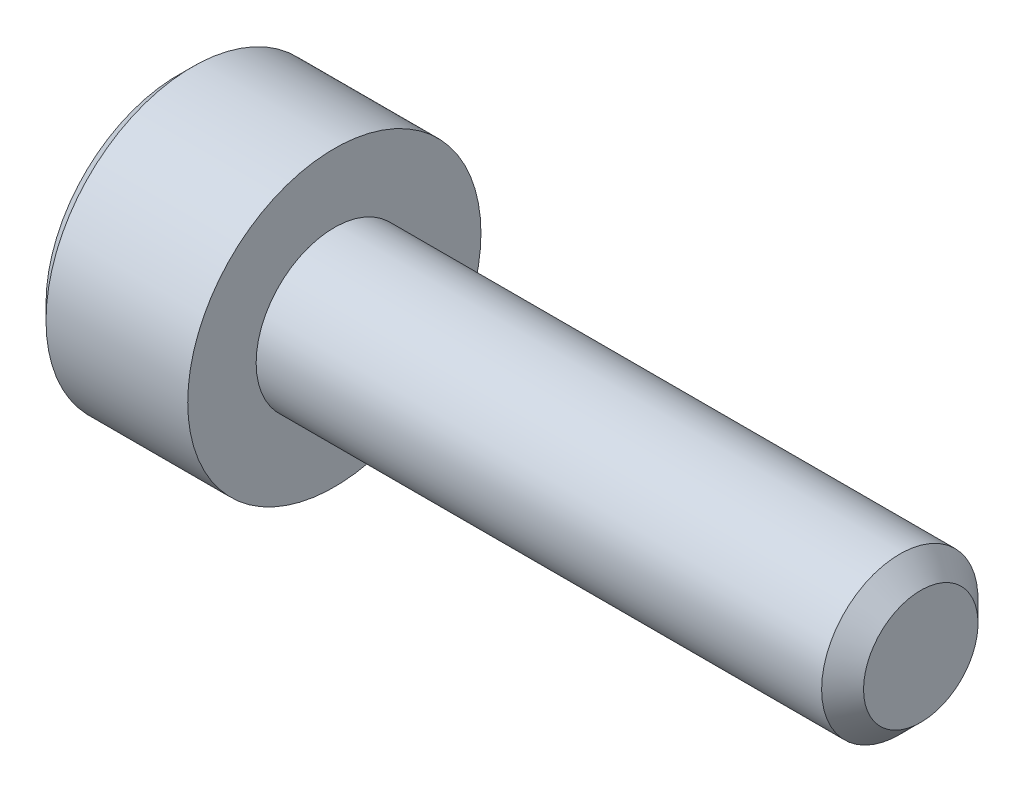
SolidWorks part; units mm, degrees
material "AISI 304"
ref_plane "正面" through (0, 0, 0) normal (0, 0, 1) x (1, 0, 0)
ref_plane "平面" through (0, 0, 0) normal (0, 1, 0) x (1, 0, 0)
ref_plane "右側面" through (0, 0, 0) normal (1, 0, 0) x (0, 0, -1)
ref_plane "Plane1" through (0, 0, 0) normal (0, 0, 1) x (1, 0, 0)
sketch "Sketch1" plane through (0, 0, 0) normal (0, 0, 1) x (1, 0, 0)
  line L0 (-1.6, 0) -> (-1.6, 1.35)
  line L1 (-1.6, 1.35) -> (-1.45, 1.5)
  line L2 (-1.45, 1.5) -> (0, 1.5)
  line L3 (0, 1.5) -> (0, 0.8)
  line L4 (0, 0.8) -> (5.7855, 0.8)
  line L5 (5.7855, 0.8) -> (6, 0.5855)
  line L6 (6, 0.5855) -> (6, 0)
  line L7 (6, 0) -> (-1.6, 0)
  line L8 (6, 0) -> (-1.6, 0) construction
revolve "Revolve1" add sketch "Sketch1" angle 360 about L8
cosmetic thread "Cosmetic Thread1" parameters "D1"=5.6276, "D2"=1.171
ref_plane "Plane2" through (-1.6, 0, 0) normal (1, 0, 0) x (0, 0, -1)
sketch "Sketch2" plane through (-1.6, 0, 0) normal (1, 0, 0) x (0, 0, -1)
  line L0 (-0.75, -0.433) -> (0, -0.866)
  line L1 (0, -0.866) -> (0.75, -0.433)
  line L2 (0.75, -0.433) -> (0.75, 0.433)
  line L3 (0.75, 0.433) -> (0, 0.866)
  line L4 (0, 0.866) -> (-0.75, 0.433)
  line L5 (-0.75, 0.433) -> (-0.75, -0.433)
extrude "Cut-Extrude1" cut sketch "Sketch2" along normal blind 0.64
